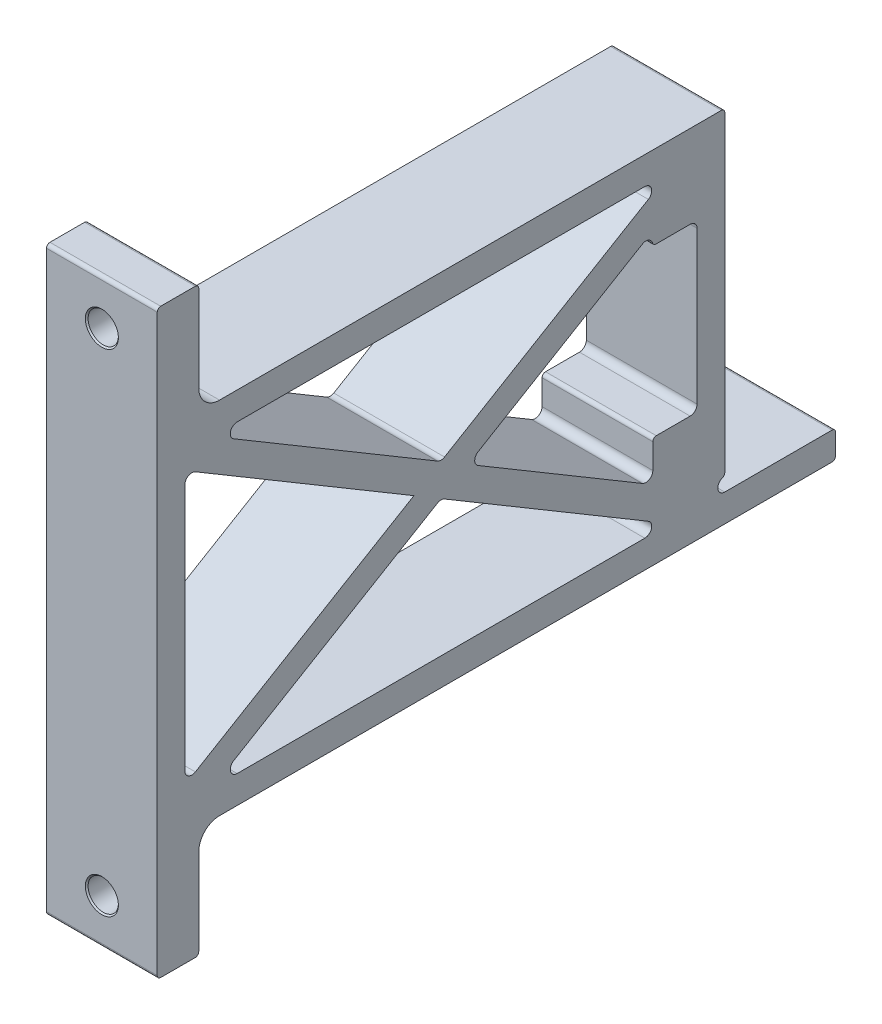
SolidWorks part; units mm, degrees
material "6061-T6 (SS)"
ref_plane "Front" through (0, 0, 0) normal (0, 0, 1) x (1, 0, 0)
ref_plane "Top" through (0, 0, 0) normal (0, 1, 0) x (1, 0, 0)
ref_plane "Right" through (0, 0, 0) normal (1, 0, 0) x (0, 0, -1)
sketch "Sketch1" plane through (0, 0, 0) normal (1, 0, 0) x (0, 0, -1)
  line L0 (0, 0) -> (-16.5171, 0) construction
  line L1 (311.15, -88.9) -> (19.05, -88.9)
  line L2 (311.15, -88.9) -> (311.15, -76.2)
  line L3 (260.35, 76.2) -> (19.05, 76.2)
  line L4 (19.05, -88.9) -> (19.05, -139.7)
  line L5 (19.05, 127) -> (0, 127)
  line L6 (19.05, 127) -> (19.05, 76.2)
  line L7 (19.05, -139.7) -> (0, -139.7)
  line L8 (0, 127) -> (0, -139.7)
  line L9 (19.05, 76.2) -> (19.05, -76.2) construction
  line L10 (311.15, -76.2) -> (260.35, -76.2)
  line L11 (260.35, -76.2) -> (260.35, 76.2)
  point P13 (19.05, 0)
  dimension "D1" = 19.05
  dimension "D2" = 260.35
  dimension "D3" = 152.4
  dimension "D4" = 165.1
  dimension "D5" = 50.8
  dimension "D9" = 50.8
extrude "Boss-Extrude1" add sketch "Sketch1" along normal mid plane 50.8
sketch "Sketch2" plane through (-25.4, 0, 0) normal (-1, 0, 0) x (0, 0, 1)
  line L29 (-126.5381, 76.2) -> (-126.5381, 63.5) construction
  line L31 (-247.65, 63.5) -> (-12.7, 63.5)
  line L34 (-247.65, 63.5) -> (-247.65, -76.2)
  line L35 (-247.65, -76.2) -> (-12.7, -76.2)
  line L36 (-12.7, 63.5) -> (-12.7, -76.2)
  line L37 (-260.35, 76.2) -> (-19.05, 76.2) construction
  line L38 (-12.7, 26.1814) -> (0, 26.1814) construction
  line L39 (0, 127) -> (0, -139.7) construction
  line L40 (-126.5381, -76.2) -> (-126.5381, -88.9) construction
  line L41 (-19.05, -88.9) -> (-311.15, -88.9) construction
  line L42 (-260.35, 52.4371) -> (-247.65, 52.4371) construction
  line L43 (-260.35, -76.2) -> (-260.35, 76.2) construction
  dimension "D1" = 12.7
extrude "Cut-Extrude1" cut sketch "Sketch2" against normal through all
sketch "Sketch3" plane through (-25.4, 0, 0) normal (-1, 0, 0) x (0, 0, 1)
  line L0 (-247.65, 63.5) -> (-12.7, -76.2)
extrude "Extrude-Thin1" add sketch "Sketch3" against normal up to surface (50.8 mm away) thin up to face at (25.4, -6.35, -130.175) thin type mid plane wall 12.7
sketch "Sketch4" plane through (-25.4, 0, 0) normal (-1, 0, 0) x (0, 0, 1)
  line L0 (-247.65, -76.2) -> (-12.7, 63.5)
  line L1 (-247.65, -76.2) -> (-25.1248, -76.2) construction
  line L2 (-12.7, -68.8123) -> (-12.7, 63.5) construction
extrude "Extrude-Thin2" add sketch "Sketch4" against normal up to surface (50.8 mm away) thin up to face at (25.4, -32.0959, -173.4749) thin type mid plane wall 12.7
fillet "Fillet5" radius 3.175 2 edges at (0, -76.2, -235.2252) (0, 63.5, -235.2252)
sketch "Sketch11" plane through (-25.4, 0, 0) normal (-1, 0, 0) x (0, 0, 1)
  line L2 (-260.35, -76.2) -> (-227.33, -76.2)
  line L3 (-260.35, -76.2) -> (-260.35, -38.1)
  line L4 (-260.35, -38.1) -> (-227.33, -38.1)
  line L5 (0, 0) -> (-55.1621, 0) construction
  line L6 (-227.33, -76.2) -> (-227.33, -38.1)
  line L8 (-227.33, -57.15) -> (-184.8339, -57.15) construction
  dimension "D1" = 57.15
  dimension "D2" = 33.02
extrude "Boss-Extrude2" add sketch "Sketch11" against normal up to surface (50.8 mm away) up to face at (25.4, 46.563, -151.6297)
mirror "Mirror2" about plane through (0, 0, 0) normal (0, 1, 0) of "Boss-Extrude2"
sketch "channel hole centers" plane through (0, 0, -260.35) normal (0, 0, -1) x (-1, 0, 0)
  line L0 (0, 57.15) -> (0, -57.15) construction
  point P2 (0, 0)
  dimension "D1" = 114.3
hole_wizard "Tapped Hole for 3/8-16 Helicoil1" positions "Sketch7" profile "Sketch6" tap size "3/8-16" standard "Helicoil® Inch"
sketch "Sketch7" plane through (-14.8769, 2.702, -260.35) normal (0, 0, -1) x (-1, 0, 0)
  point P0 (-14.8769, 54.448)
  point P1 (-14.8769, -59.852)
sketch "Sketch6" plane through (0, 57.15, -260.35) normal (1, 0, 0) x (0, 1, 0)
  line L0 (0, 0) -> (0, 32.2395)
  line L1 (0, 32.2395) -> (5.0419, 29.21)
  line L2 (5.0419, 29.21) -> (5.0419, 1.4376)
  line L3 (5.0419, 1.4376) -> (6.4795, 0)
  line L5 (6.4795, 0) -> (0, 0)
  line L6 (-5.0419, 1.4376) -> (-6.4795, 0) construction
  line L10 (0, 32.2395) -> (-5.0419, 29.21) construction
  line L11 (0, -6.35) -> (0, 107.95) construction
  dimension "Tap Drill Dia." = 10.0838
  dimension "Tap Drill Depth" = 29.21
  dimension "Near C'Sink Dia." = 12.9591
  dimension "Near C'Sink Angle" = 90
  dimension "Drill Angle" = 118
cosmetic thread "Hole Thread1"
cosmetic thread "Hole Thread2"
sketch "Sketch12" plane through (-25.4, 0, 0) normal (-1, 0, 0) x (0, 0, 1)
  line L0 (-260.35, -76.2) -> (-260.35, 76.2) construction
  line L1 (-311.15, -76.2) -> (-260.35, -76.2) construction
  line L2 (-260.35, -76.2) -> (-260.35, -69.85)
  arc A0 (-260.35, -76.2) -> (-260.35, -69.85) centre (-260.35, -73.025) ccw
  dimension "D1" = 6.35
extrude "Cut-Extrude2" cut sketch "Sketch12" against normal through all
fillet "Fillet1" radius 3.175 11 edges at (0, 1.0377, -130.175) (0, -13.7377, -130.175) (0, -6.35, -142.5998) (0, 63.5, -25.1248) (0, 56.1123, -12.7) (0, -68.8123, -12.7) (0, -76.2, -25.1248) (0, -56.7301, -227.33) (0, -38.1, -247.65) (0, 38.1, -247.65) (0, 44.0301, -227.33)
fillet "Fillet2" radius 1.5875 10 edges at (0, 127, 0) (0, 127, -19.05) (0, -139.7, 0) (0, -139.7, -19.05) (0, -88.9, -311.15) (0, -76.2, -311.15) (0, 76.2, -260.35) (0, 38.1, -227.33) (0, -38.1, -227.33) (0, -69.85, -260.35)
fillet "Fillet3" radius 9.525 2 edges at (0, 76.2, -19.05) (0, -88.9, -19.05)
sketch "mount hole centers" plane through (0, 0, -19.05) normal (0, 0, -1) x (-1, 0, 0)
  line L0 (25.4, 85.725) -> (-25.4, 127) construction
  line L1 (25.4, -98.425) -> (-25.4, -139.7) construction
  point P8 (0, 106.3625)
  point P9 (0, -119.0625)
  point P10 (0, -119.0625)
  point P11 (0, 106.3625)
hole_wizard "1/2 Clearance Hole1" positions "Sketch10" profile "Sketch9" hole size "1/2" standard "Ansi Inch" end condition up to next
sketch "Sketch10" plane through (0, 0, -19.05) normal (0, 0, -1) x (-1, 0, 0)
  point P0 (0, 106.3625)
  point P1 (0, -119.0625)
sketch "Sketch9" plane through (0, 106.3625, -19.05) normal (1, 0, 0) x (0, 1, 0)
  line L0 (0, 0) -> (0, 19.05)
  line L1 (0, 19.05) -> (7.5806, 19.05)
  line L2 (6.9456, 18.415) -> (6.9456, 0.635)
  line L3 (6.9456, 0.635) -> (7.5806, 0)
  line L5 (7.5806, 0) -> (0, 0)
  line L6 (-6.9456, 0.635) -> (-7.5806, 0) construction
  line L7 (7.5806, 19.05) -> (6.9456, 18.415)
  line L8 (-7.5806, 19.05) -> (-6.9456, 18.415) construction
  line L11 (0, -6.35) -> (0, 107.95) construction
  dimension "Thru Hole Dia." = 13.8913
  dimension "Thru Hole Depth" = 19.05
  dimension "Near C'Sink Dia." = 15.1613
  dimension "Near C'Sink Angle" = 90
  dimension "Far C'Sink Dia." = 15.1613
  dimension "Far C'Sink Angle" = 90
